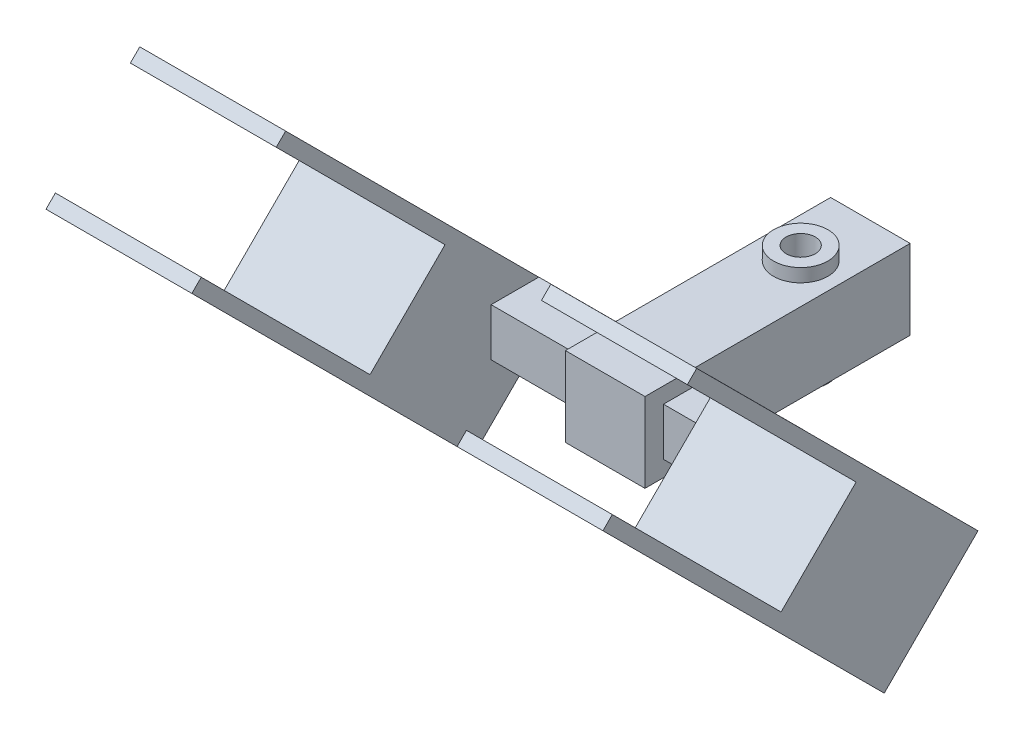
SolidWorks part; units mm, degrees
ref_plane "Front" through (0, 0, 0) normal (0, 0, 1) x (1, 0, 0)
ref_plane "Top" through (0, 0, 0) normal (0, 1, 0) x (1, 0, 0)
ref_plane "Right" through (0, 0, 0) normal (1, 0, 0) x (0, 0, -1)
sketch "草图2" plane through (0, 0, 0) normal (0, 0, 1) x (1, 0, 0)
  line L1 (-15, -15) -> (15, -15)
  line L2 (-15, -15) -> (-15, 15)
  line L3 (-15, 15) -> (15, 15)
  line L4 (15, -15) -> (15, 15)
  line L5 (-15, -15) -> (15, 15) construction
  line L6 (-15, 15) -> (15, -15) construction
  point P0 (0, 0)
  dimension "D1" = 30
  dimension "D2" = 30
extrude "凸台-拉伸1" add sketch "草图2" along normal blind 100
sketch "草图3" plane through (15, 0, 0) normal (1, 0, 0) x (0, 0, -1)
  line L1 (-75.019, 9) -> (-93.019, 9)
  line L2 (-75.019, 9) -> (-75.019, -9)
  line L3 (-75.019, -9) -> (-93.019, -9)
  line L4 (-93.019, 9) -> (-93.019, -9)
  line L5 (-75.019, 9) -> (-93.019, -9) construction
  line L6 (-75.019, -9) -> (-93.019, 9) construction
  point P0 (-84.019, 0)
  dimension "D1" = 18
  dimension "D2" = 18
extrude "凸台-拉伸2" add sketch "草图3" along normal blind 35
pattern_circular "阵列(圆周)1" count 2 over 360 about axis through (0, 0, 0) along (0, 0, 1) of "凸台-拉伸2"
sketch "草图4" plane through (0, 15, 0) normal (0, 1, 0) x (1, 0, 0)
  circle A0 centre (0, -26.2854) radius 10.2542
  circle A1 centre (0, -26.2854) radius 5.2542
  dimension "D1" = 20.5085
  dimension "D2" = 5
extrude "凸台-拉伸4" add sketch "草图4" along normal blind 5 contours A0
sketch "草图5" plane through (0, 20, 0) normal (0, 1, 0) x (1, 0, 0)
  circle A0 centre (0, -26.2854) radius 5.5
  dimension "D1" = 11
extrude "切除-拉伸2" cut sketch "草图5" against normal blind 15
pattern_circular "阵列(圆周)3" count 2 over 360 about axis through (0, 0, 100) along (0, 0, -1) of "凸台-拉伸4"
pattern_circular "阵列(圆周)4" count 2 over 360 about axis through (0, 0, 100) along (0, 0, -1) of "切除-拉伸2"
sketch "草图6" plane through (50, 0, 0) normal (1, 0, 0) x (0, 0, -1)
  line L0 (-93.019, 9) -> (-73.4124, -10.6066) construction
  line L1 (-84.6537, 17.1572) -> (-93.019, 9) construction
  line L2 (-73.4124, -10.6066) -> (-64.432, -1.6261) construction
  line L3 (-64.432, -1.6261) -> (-106.8584, 40.8003)
  line L4 (-106.8584, 40.8003) -> (-171.3221, -23.6634) construction
  line L5 (-106.8584, 40.8003) -> (-142.2137, 5.4449)
  line L6 (-142.2137, 5.4449) -> (-99.7873, -36.9815)
  line L7 (-99.7873, -36.9815) -> (-64.432, -1.6261)
  dimension "D1" = 60
  dimension "D2" = 15
  dimension "D3" = 50
extrude "凸台-拉伸5" add sketch "草图6" along normal blind 55
pattern_linear "阵列(线性)1" count 2 spacing 155 along (-1, 0, 0) of "凸台-拉伸5"
sketch "草图7" plane through (0, 73.8293, 73.8293) normal (0, 0.7071, 0.7071) x (1, 0, 0)
  line L0 (105, -46.7101) -> (105, -96.7101) construction
  line L1 (105, -91.7101) -> (50, -91.7101)
  line L2 (105, -91.7101) -> (105, -96.7101)
  line L3 (105, -96.7101) -> (50, -96.7101)
  line L4 (50, -91.7101) -> (50, -96.7101)
  line L5 (105, -96.7101) -> (50, -96.7101) construction
  line L6 (50, -46.7101) -> (50, -96.7101) construction
  line L7 (105, -46.7101) -> (50, -46.7101) construction
  line L8 (105, -46.7101) -> (50, -46.7101)
  line L9 (105, -46.7101) -> (105, -51.7101)
  line L10 (105, -51.7101) -> (50, -51.7101)
  line L11 (50, -46.7101) -> (50, -51.7101)
  line L12 (0, 45.1495) -> (0, -147.3837) construction
  line L13 (-105, -96.7101) -> (-50, -96.7101)
  line L14 (-50, -91.7101) -> (-50, -96.7101)
  line L15 (-105, -91.7101) -> (-50, -91.7101)
  line L16 (-105, -91.7101) -> (-105, -96.7101)
  line L17 (-105, -51.7101) -> (-50, -51.7101)
  line L18 (-50, -46.7101) -> (-50, -51.7101)
  line L19 (-105, -46.7101) -> (-50, -46.7101)
  line L20 (-105, -46.7101) -> (-105, -51.7101)
  dimension "D1" = 5
  dimension "D2" = 5
  dimension "D3" = 0
extrude "凸台-拉伸6" add sketch "草图7" along normal blind 90
